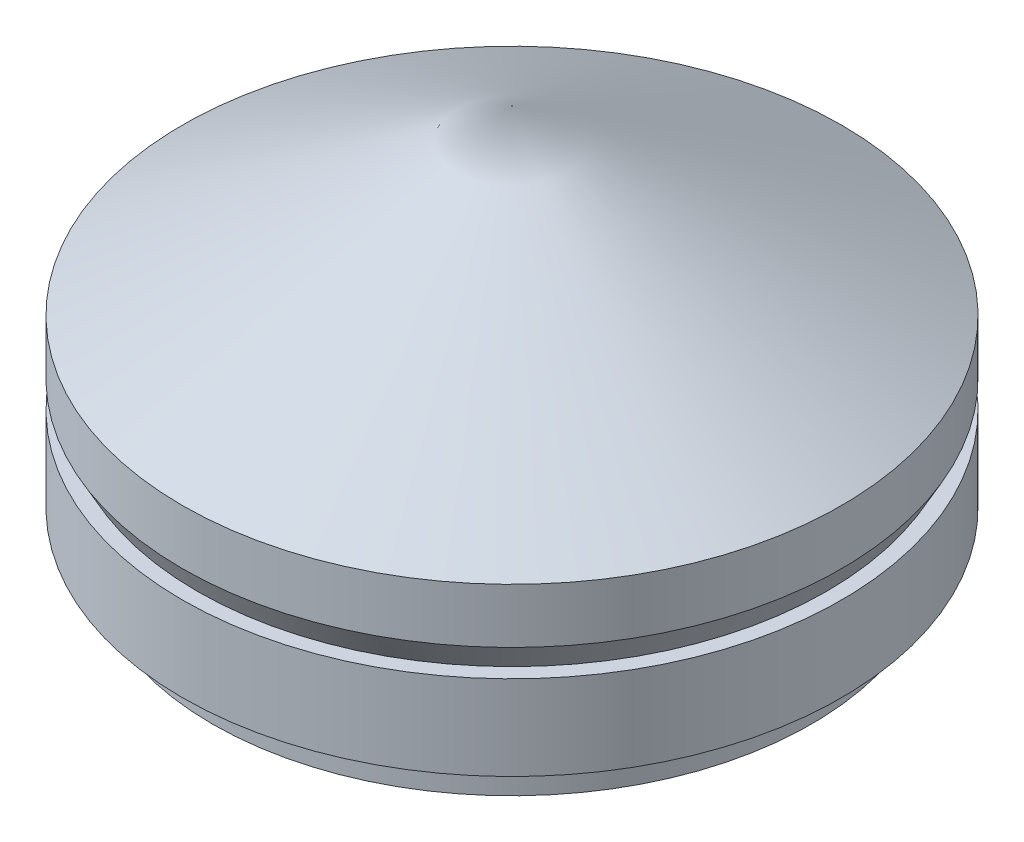
SolidWorks part; units mm, degrees
ref_plane "Front Plane" through (0, 0, 0) normal (0, 0, 1) x (1, 0, 0)
ref_plane "Top Plane" through (0, 0, 0) normal (0, 1, 0) x (1, 0, 0)
ref_plane "Right Plane" through (0, 0, 0) normal (1, 0, 0) x (0, 0, -1)
sketch "Sketch7" plane through (0, 0, 0) normal (0, 0, 1) x (1, 0, 0)
  line L0 (0, 55.1341) -> (0, 48.7248)
  line L1 (0, 55.1341) -> (-6.075, 51.7928)
  line L2 (-6.075, 51.7928) -> (-6.075, 50.7848)
  line L3 (-6.075, 50.7848) -> (-5.8, 50.2848)
  line L4 (-5.8, 50.2848) -> (-6.075, 50.2848)
  line L5 (-6.075, 50.2848) -> (-6.075, 48.7248)
  line L6 (-6.075, 48.7248) -> (0, 48.7248)
  dimension "D1" = 6.075
  dimension "D2" = 0.5
  dimension "D3" = 1.56
  dimension "D4" = 5.8
revolve "Revolve1" add sketch "Sketch7" angle 360 about L0
sketch "Sketch8" plane through (0, 48.7248, 0) normal (0, -1, 0) x (1, 0, 0)
  circle A0 centre (0, 0) radius 5.52
extrude "Boss-Extrude2" add sketch "Sketch8" along normal blind 0.7
